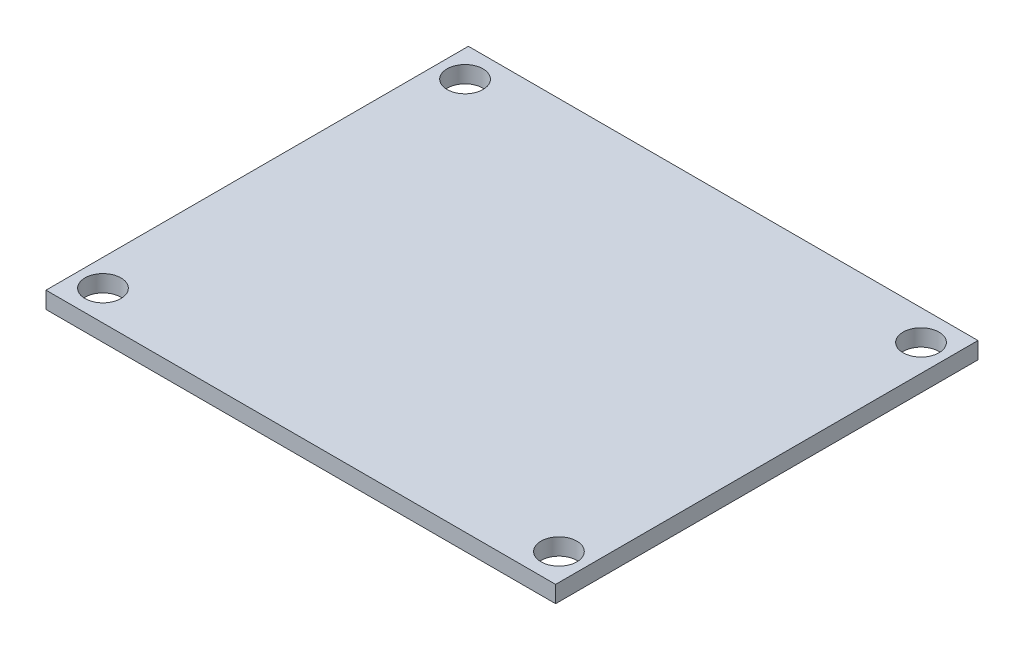
SolidWorks part; units mm, degrees
ref_plane "Front Plane" through (0, 0, 0) normal (0, 0, 1) x (1, 0, 0)
ref_plane "Top Plane" through (0, 0, 0) normal (0, 1, 0) x (1, 0, 0)
ref_plane "Right Plane" through (0, 0, 0) normal (1, 0, 0) x (0, 0, -1)
sketch "Sketch1" plane through (0, 0, 0) normal (0, 1, 0) x (1, 0, 0)
  line L1 (-42.7686, 22.2552) -> (5.4914, 22.2552)
  line L2 (-42.7686, 22.2552) -> (-42.7686, -17.7448)
  line L3 (-42.7686, -17.7448) -> (5.4914, -17.7448)
  line L4 (5.4914, 22.2552) -> (5.4914, -17.7448)
  dimension "D1" = 48.26
  dimension "D2" = 40
extrude "Boss-Extrude1" add sketch "Sketch1" along normal blind 1.5875
hole_wizard "Clearance hole for 3MM screw" positions "Sketch10" profile "Sketch9" hole size "M3" standard "Ansi Metric"
sketch "Sketch10" plane through (0, 1.5875, 0) normal (0, 1, 0) x (-1, 0, 0)
  line L0 (42.7686, -22.2552) -> (42.7686, 17.7448) construction
  line L3 (-5.4914, -22.2552) -> (42.7686, -22.2552) construction
  point P0 (40.2286, -19.4002)
  dimension "D1" = 2.54
  dimension "D2" = 2.855
sketch "Sketch9" plane through (-40.2286, 1.5875, -19.4002) normal (1, 0, 0) x (0, 0, 1)
  line L0 (0, 0) -> (0, 13.7215)
  line L1 (0, 13.7215) -> (1.7, 12.7)
  line L2 (1.7, 12.7) -> (1.7, 0)
  line L5 (1.7, 0) -> (0, 0)
  line L10 (0, 13.7215) -> (-1.7, 12.7) construction
  line L11 (0, -6.35) -> (0, 107.95) construction
  dimension "Hole Dia." = 3.4
  dimension "Hole Depth" = 12.7
  dimension "Drill Angle" = 118
pattern_linear "LPattern1" count 2 spacing 43.18 along (1, 0, 0) count 2 spacing 34.29 along (0, 0, 1) of "Clearance hole for 3MM screw"
equation "\"D1@Sketch10\" = (\"D1@Sketch1\"-\"D3@LPattern1\")/2"
equation "\"D2@Sketch10\" = (\"D2@Sketch1\"-\"D4@LPattern1\")/2"
